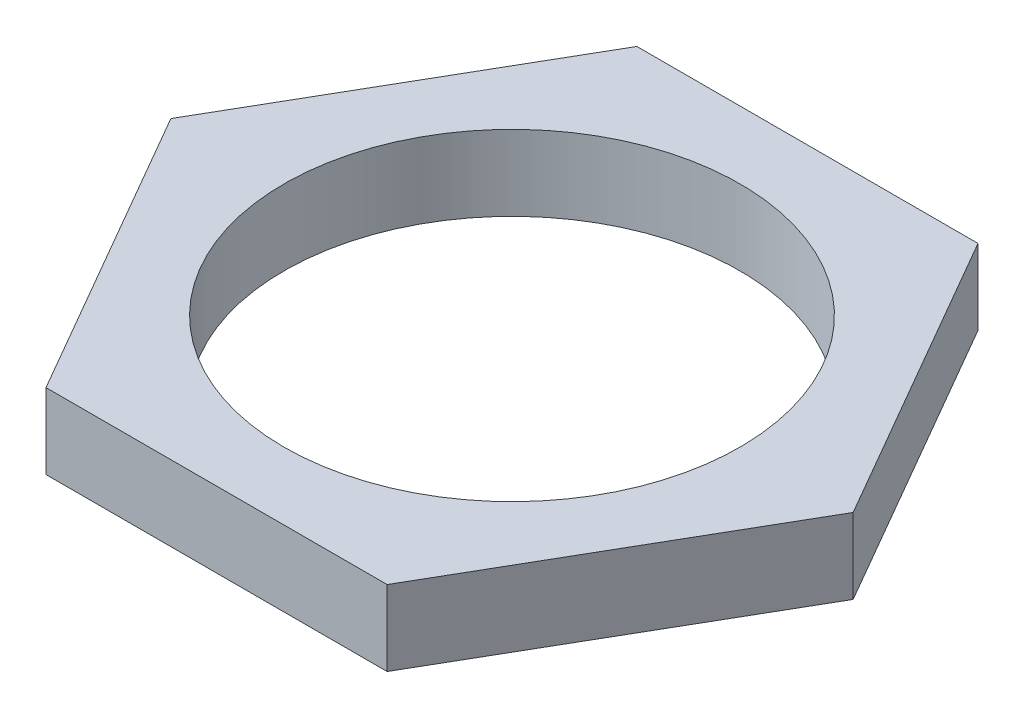
SolidWorks part; units mm, degrees
material "Vanadium"
ref_plane "Front Plane" through (0, 0, 0) normal (0, 0, 1) x (1, 0, 0)
ref_plane "Top Plane" through (0, 0, 0) normal (0, 1, 0) x (1, 0, 0)
ref_plane "Right Plane" through (0, 0, 0) normal (1, 0, 0) x (0, 0, -1)
sketch "Sketch1" plane through (0, 0, 0) normal (0, 1, 0) x (1, 0, 0)
  line L1 (-8.6025, 0) -> (-4.3013, -7.45)
  line L2 (-4.3013, -7.45) -> (4.3013, -7.45)
  line L3 (4.3013, -7.45) -> (8.6025, 0)
  line L4 (8.6025, 0) -> (4.3013, 7.45)
  line L5 (4.3013, 7.45) -> (-4.3013, 7.45)
  line L6 (-4.3013, 7.45) -> (-8.6025, 0)
  circle A0 centre (0, 0) radius 7.45 construction
  circle A1 centre (0, 0) radius 5.75
  dimension "D2" = 11.5
  dimension "D1" = 14.9
extrude "Boss-Extrude1" add sketch "Sketch1" along normal blind 1.9
thread "Thread1" pitch 0.7937 start angle 0, offset 1, length 10, pitch 0.7937, diameter 11.5
ref_plane "Plane1" through (-5.75, 2.9, 0) normal (0, 0, 1) x (-1, 0, 0)
sketch "Thread Profile1" plane through (-5.75, 2.9, 0) normal (0, 0, 1) x (-1, 0, 0)
  line L0 (0, 0) -> (0, 0.7937) construction
  line L11 (0, 0) -> (0, 0.6945)
  line L12 (0, 0.6945) -> (-0.4296, 0.4465)
  line L13 (-0.4296, 0.4465) -> (-0.4296, 0.248)
  line L15 (-0.4296, 0.248) -> (0, 0)
  line L17 (-0.4296, 0.3473) -> (0, 0.3473) construction
  point P2 (0, 0)
  dimension "Pitch" = 0.7937
  dimension "Profile_Angle" = 60
  dimension "Profile_Land" = 0.1984
  dimension "Profile_Height" = 0.4296
